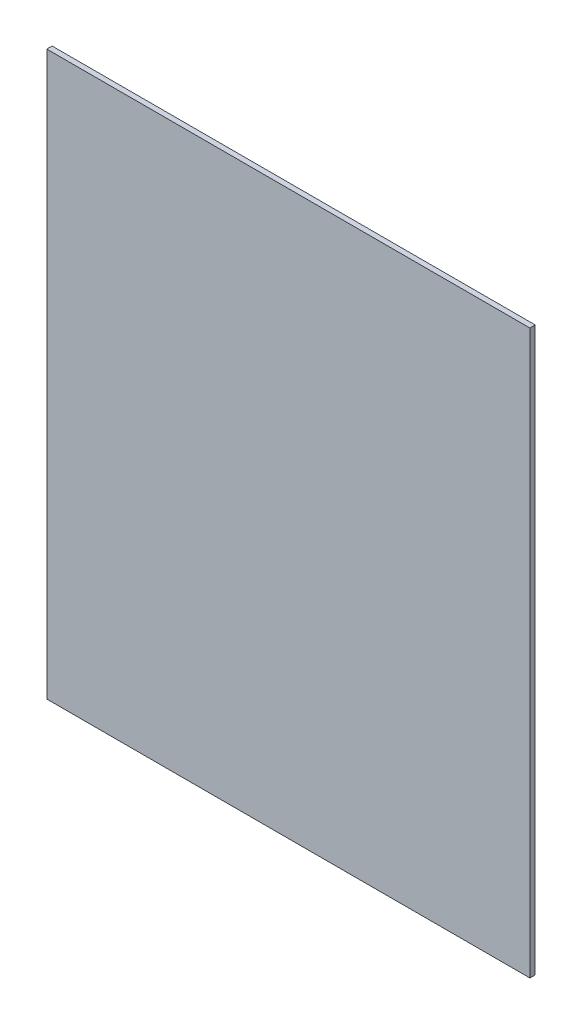
SolidWorks part; units mm, degrees
material "PC High Viscosity"
ref_plane "Front Plane" through (0, 0, 0) normal (0, 0, 1) x (1, 0, 0)
ref_plane "Top Plane" through (0, 0, 0) normal (0, 1, 0) x (1, 0, 0)
ref_plane "Right Plane" through (0, 0, 0) normal (1, 0, 0) x (0, 0, -1)
sketch "Sketch3" plane through (0, 0, 0) normal (0, 0, 1) x (1, 0, 0)
  line L1 (-9109.5159, 9521.1484) -> (-10019.275, 9521.1484)
  line L2 (-9109.5159, 9521.1484) -> (-9109.5159, 8461.1484)
  line L3 (-9109.5159, 8461.1484) -> (-10019.275, 8461.1484)
  line L4 (-10019.275, 9521.1484) -> (-10019.275, 8461.1484)
extrude "Boss-Extrude1" add sketch "Sketch3" along normal blind 10
